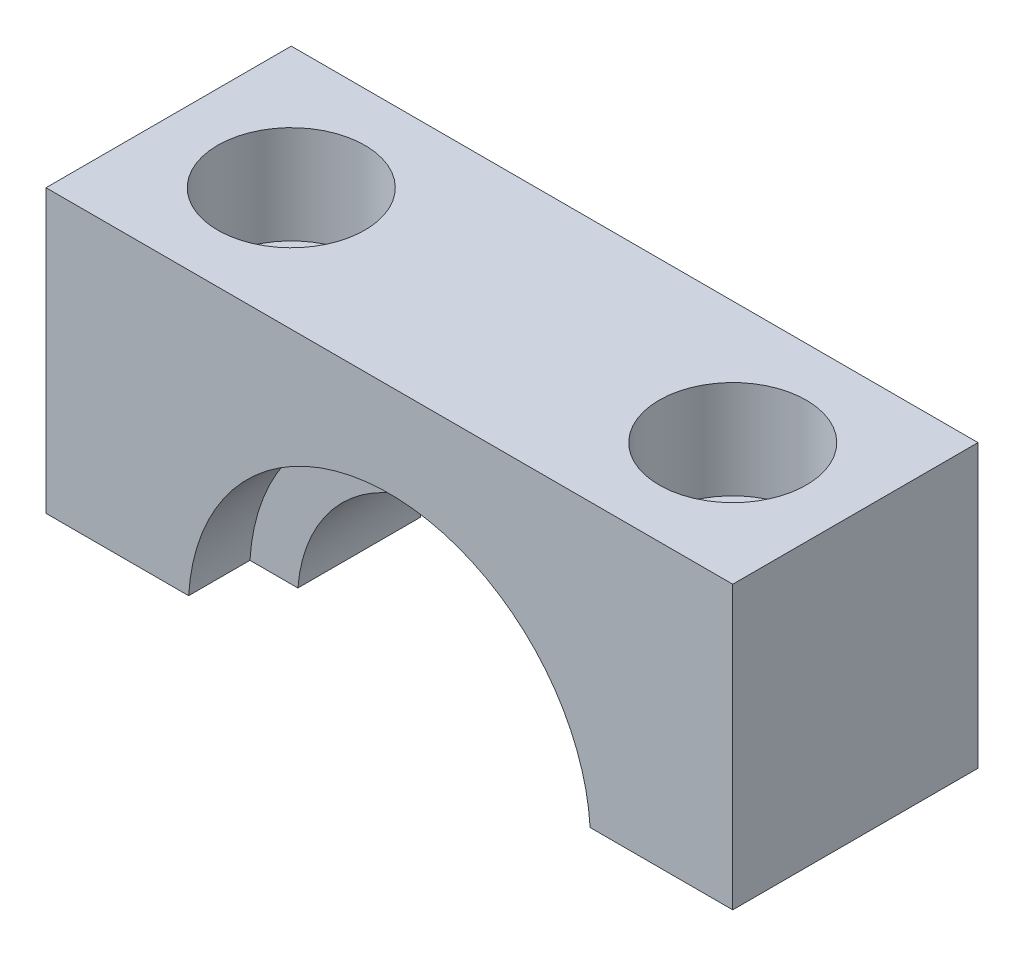
SolidWorks part; units mm, degrees
ref_plane "Plano frontal" through (0, 0, 0) normal (0, 0, 1) x (1, 0, 0)
ref_plane "Plano superior" through (0, 0, 0) normal (0, 1, 0) x (1, 0, 0)
ref_plane "Plano direito" through (0, 0, 0) normal (1, 0, 0) x (0, 0, -1)
sketch "Esboço1" plane through (0, 0, 0) normal (0, 0, 1) x (1, 0, 0)
  line L0 (-6.23, 0.5) -> (-14, 0.5)
  line L1 (-14, 0.5) -> (-14, 12)
  line L2 (-14, 12) -> (14, 12)
  line L3 (14, 12) -> (14, 0.5)
  line L4 (14, 0.5) -> (6.23, 0.5)
  arc A0 (6.23, 0.5) -> (-6.23, 0.5) centre (0, 0) ccw
  dimension "D1" = 6.25
  dimension "D2" = 28
  dimension "D3" = 11.5
  dimension "D4" = 12
extrude "Ressalto-extrusão1" add sketch "Esboço1" along normal mid plane 5
sketch "Esboço3" plane through (0, 0, 0) normal (0, 0, 1) x (1, 0, 0)
  line L0 (-14, 12) -> (-14, 0.5)
  line L1 (-14, 0.5) -> (-8.1847, 0.5)
  line L2 (8.1847, 0.5) -> (14, 0.5)
  line L3 (14, 0.5) -> (14, 12)
  line L4 (14, 12) -> (-14, 12)
  arc A0 (8.1847, 0.5) -> (-8.1847, 0.5) centre (0, 0) ccw
  dimension "D1" = 8.2
extrude "Ressalto-extrusão2" add sketch "Esboço3" along normal mid plane 10
sketch "Esboço2" plane through (0, 0.5, 0) normal (0, -1, 0) x (1, 0, 0)
  line L0 (0, 0) -> (0, 9.5392) construction
  line L1 (-6.23, 2.5) -> (-6.23, -2.5) construction
  circle A0 centre (-9, 0) radius 1.65
  circle A1 centre (9, 0) radius 1.65
  point P7 (-6.23, 0)
  dimension "D2" = 3.3
  dimension "D1" = 18
extrude "Corte-extrusão1" cut sketch "Esboço2" against normal blind 15
sketch "Esboço4" plane through (0, 12, 0) normal (0, 1, 0) x (1, 0, 0)
  circle A0 centre (-9, 0) radius 3
  circle A1 centre (9, 0) radius 3
  dimension "D1" = 6
extrude "Corte-extrusão2" cut sketch "Esboço4" against normal blind 4
